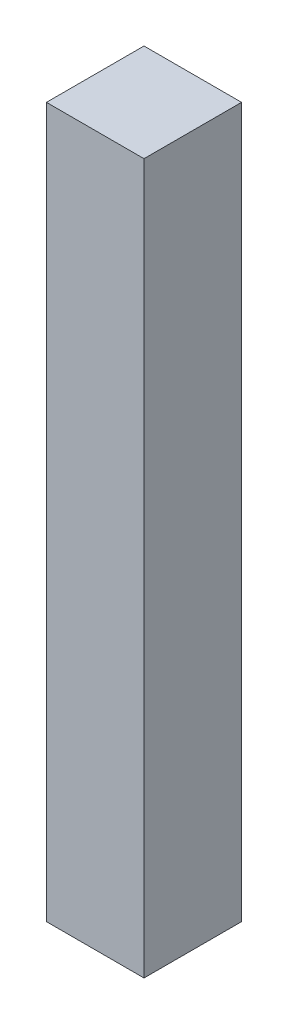
SolidWorks part; units mm, degrees
ref_plane "Front Plane" through (0, 0, 0) normal (0, 0, 1) x (1, 0, 0)
ref_plane "Top Plane" through (0, 0, 0) normal (0, 1, 0) x (1, 0, 0)
ref_plane "Right Plane" through (0, 0, 0) normal (1, 0, 0) x (0, 0, -1)
sketch "Sketch1" plane through (0, 0, 0) normal (0, 1, 0) x (1, 0, 0)
  line L1 (0, 0) -> (2.75, 0)
  line L2 (0, 0) -> (0, 2.75)
  line L3 (0, 2.75) -> (2.75, 2.75)
  line L4 (2.75, 0) -> (2.75, 2.75)
  dimension "D1" = 2.75
  dimension "D2" = 2.75
extrude "Boss-Extrude1" add sketch "Sketch1" along normal blind 20
